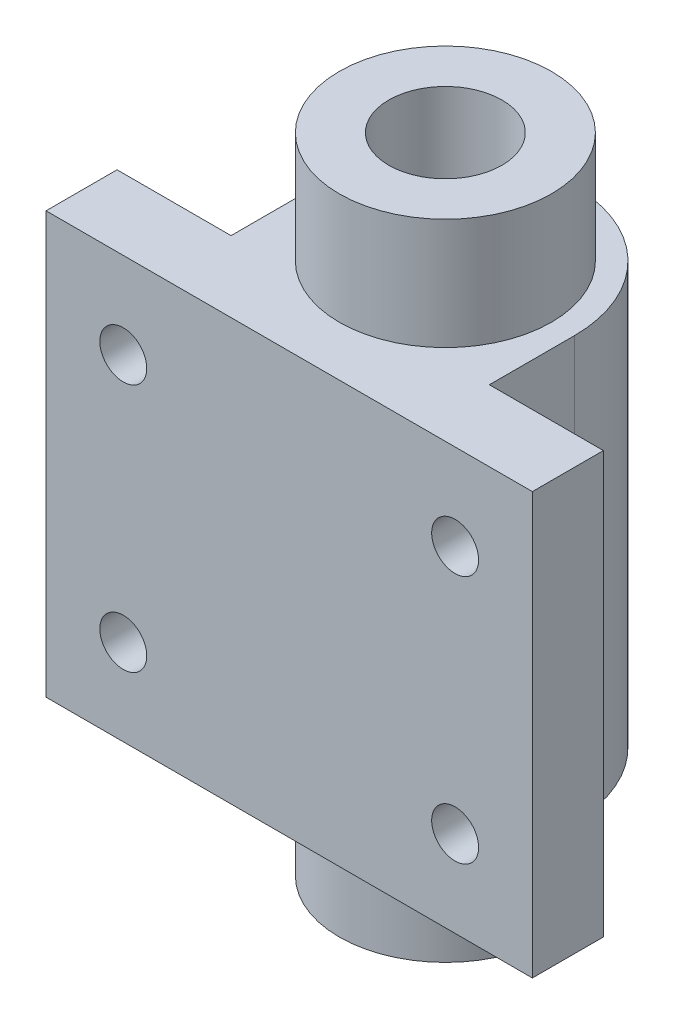
SolidWorks part; units mm, degrees
ref_plane "Front Plane" through (0, 0, 0) normal (0, 0, 1) x (1, 0, 0)
ref_plane "Top Plane" through (0, 0, 0) normal (0, 1, 0) x (1, 0, 0)
ref_plane "Right Plane" through (0, 0, 0) normal (1, 0, 0) x (0, 0, -1)
sketch "Sketch1" plane through (0, 0, 0) normal (0, 1, 0) x (1, 0, 0)
  line L0 (0, 0) -> (17.19, 0)
  line L1 (17.19, 0) -> (17.19, 5.02)
  line L2 (17.19, 5.02) -> (9.13, 5.02)
  line L3 (9.13, 5.02) -> (9.13, 11.04)
  line L4 (0, 0) -> (-17.19, 0)
  line L5 (-17.19, 0) -> (-17.19, 5.02)
  line L6 (-17.19, 5.02) -> (-9.13, 5.02)
  line L7 (-9.13, 5.02) -> (-9.13, 11.04)
  line L8 (0, 0) -> (0, 11.04) construction
  circle A0 centre (0, 11.04) radius 4
  arc A1 (9.13, 11.04) -> (-9.13, 11.04) centre (0, 11.04) ccw
  dimension "D2" = 8
  dimension "D1" = 11.04
  dimension "D3" = 5.02
  dimension "D4" = 17.19
  dimension "D5" = 8.06
extrude "Boss-Extrude1" add sketch "Sketch1" along normal blind 29.78
sketch "Sketch2" plane through (0, 29.78, 0) normal (0, 1, 0) x (1, 0, 0)
  circle A0 centre (0, 11.04) radius 4
  circle A1 centre (0, 11.04) radius 7.5
  dimension "D1" = 15
  dimension "D2" = 8
extrude "Boss-Extrude2" add sketch "Sketch2" along normal blind 7.86
sketch "Sketch3" plane through (0, 0, 0) normal (0, -1, 0) x (1, 0, 0)
  circle A0 centre (0, -11.04) radius 4
  circle A1 centre (0, -11.04) radius 7.5
  dimension "D1" = 15
  dimension "D2" = 8
extrude "Boss-Extrude3" add sketch "Sketch3" along normal blind 7.86
sketch "Sketch4" plane through (0, 0, 0) normal (0, 0, 1) x (1, 0, 0)
  line L0 (0, 0) -> (0, 29.78) construction
  line L1 (-17.19, 29.78) -> (17.19, 29.78) construction
  line L2 (-17.19, 14.89) -> (17.19, 14.89) construction
  line L3 (-17.19, 29.78) -> (-17.19, 0) construction
  line L4 (17.19, 29.78) -> (17.19, 0) construction
  circle A0 centre (-11.73, 23.69) radius 1.66
  circle A1 centre (11.73, 23.69) radius 1.66
  circle A2 centre (11.73, 6.09) radius 1.66
  circle A3 centre (-11.73, 6.09) radius 1.66
  dimension "D1" = 5.46
  dimension "D3" = 3.32
  dimension "D2" = 6.09
extrude "Cut-Extrude1" cut sketch "Sketch4" against normal through all
